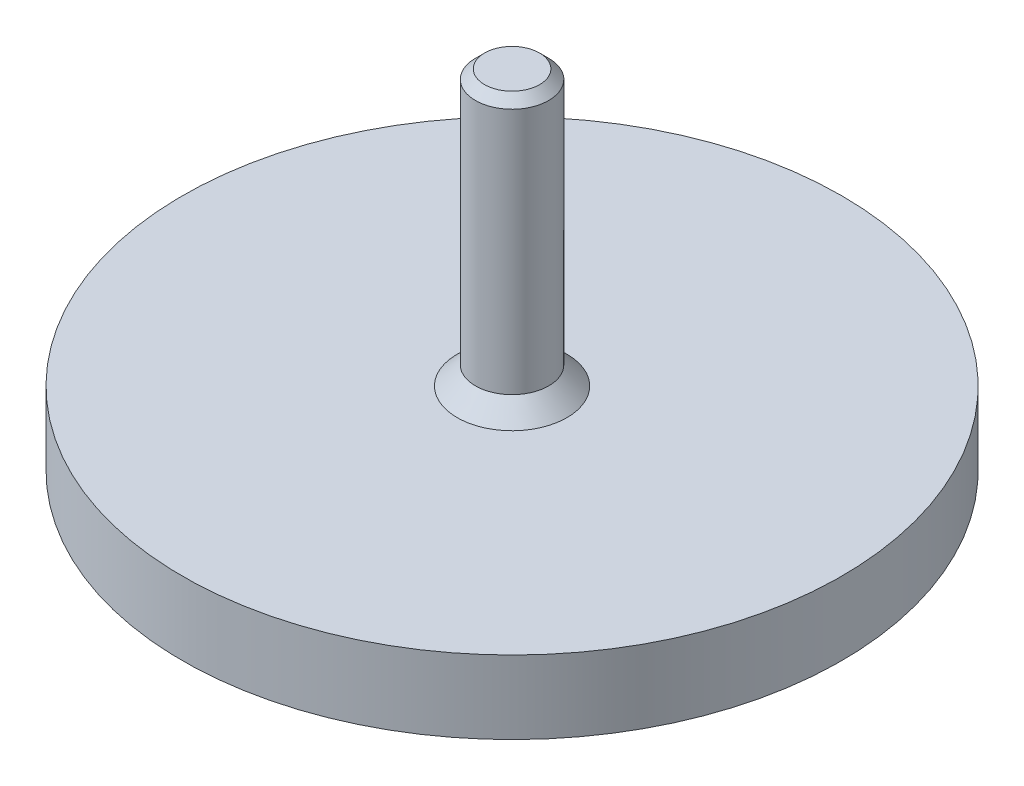
SolidWorks part; units mm, degrees
ref_plane "Face" through (0, 0, 0) normal (0, 0, 1) x (1, 0, 0)
ref_plane "Dessus" through (0, 0, 0) normal (0, 1, 0) x (1, 0, 0)
ref_plane "Droite" through (0, 0, 0) normal (1, 0, 0) x (0, 0, -1)
sketch "Esquisse1" plane through (0, 0, 0) normal (0, 0, 1) x (1, 0, 0)
  line L0 (0, 0) -> (0, 95.3652) construction
  line L1 (0, 0) -> (-18, 0)
  line L2 (-18, 4) -> (-2, 4)
  line L3 (-2, 4) -> (-2, 19)
  line L4 (-2, 19) -> (0, 19)
  line L5 (0, 0) -> (0, 19)
  line L7 (-18, 0) -> (-18, 4)
  line L8 (-18, 4) -> (-18, 0) construction
  line L9 (0, 2) -> (-18, 2) construction
  dimension "D1" = 2
  dimension "D2" = 2
  dimension "D3" = 15
  dimension "D4" = 18
revolve "Révolution1" add sketch "Esquisse1" angle 360 about L0
chamfer "Chanfrein1" distance 1 angle 45 1 edges at (0, 4, -2)
chamfer "Chanfrein2" distance 0.5 angle 45 1 edges at (0, 19, -2)
